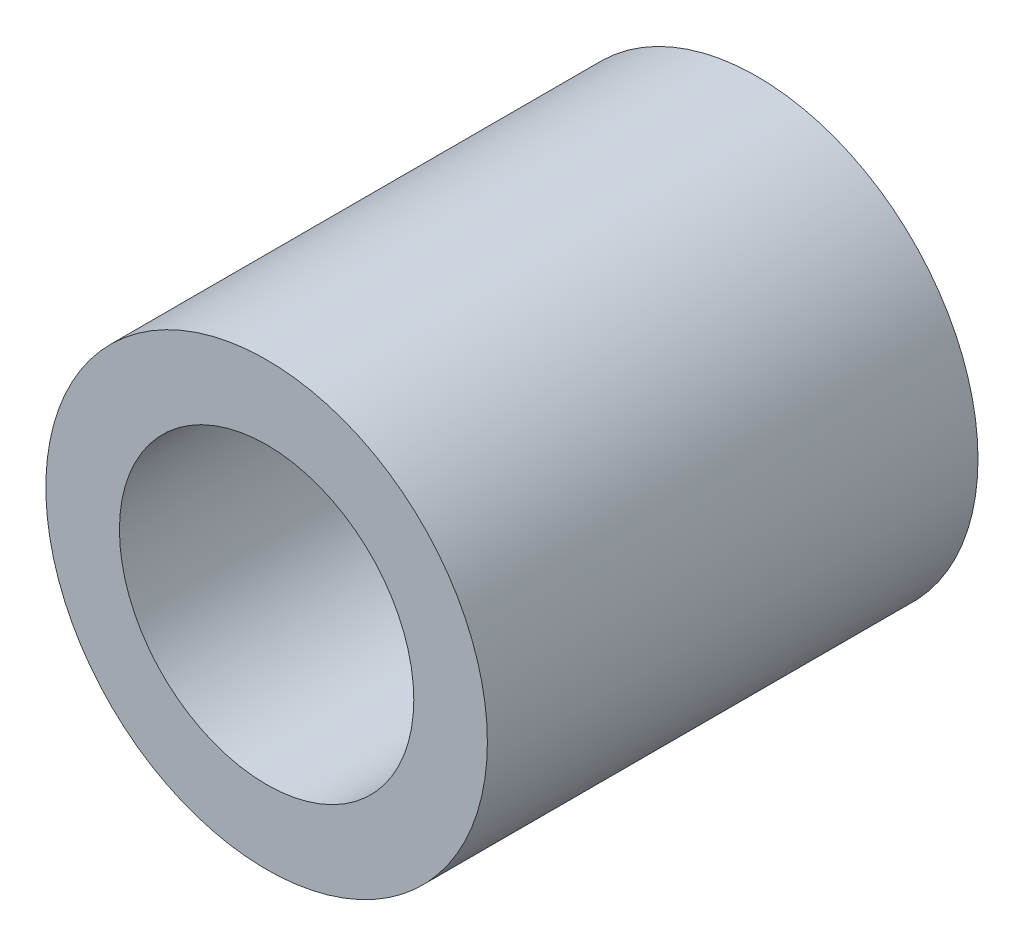
SolidWorks part; units mm, degrees
material "Alumina"
ref_plane "Front Plane" through (0, 0, 0) normal (0, 0, 1) x (1, 0, 0)
ref_plane "Top Plane" through (0, 0, 0) normal (0, 1, 0) x (1, 0, 0)
ref_plane "Right Plane" through (0, 0, 0) normal (1, 0, 0) x (0, 0, -1)
sketch "Sketch1" plane through (0, 0, 0) normal (0, 0, 1) x (1, 0, 0)
  circle A0 centre (0, -148.5737) radius 4.5
  circle A1 centre (0, 0) radius 4.5
  circle A2 centre (0, 0) radius 3
  dimension "D1" = 9
  dimension "D2" = 6
extrude "Boss-Extrude1" add sketch "Sketch1" along normal blind 10 contours A1 | A2
